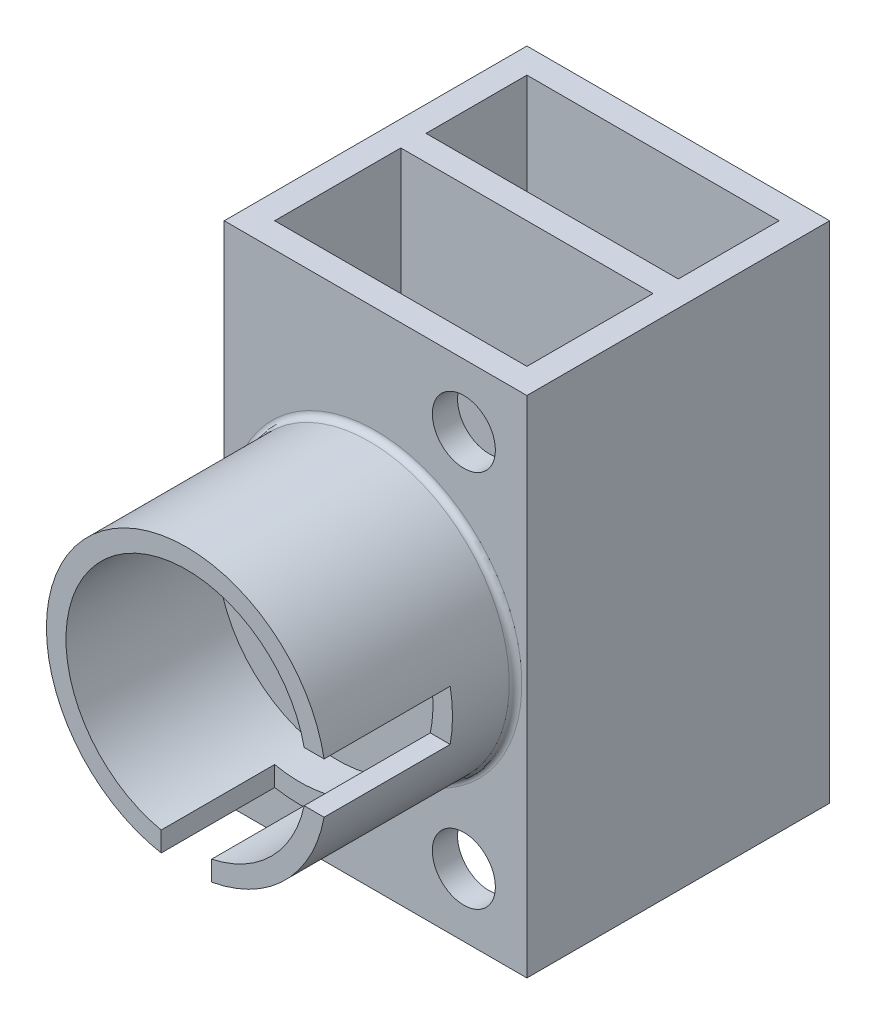
SolidWorks part; units mm, degrees
ref_plane "Front Plane" through (0, 0, 0) normal (0, 0, 1) x (1, 0, 0)
ref_plane "Top Plane" through (0, 0, 0) normal (0, 1, 0) x (1, 0, 0)
ref_plane "Right Plane" through (0, 0, 0) normal (1, 0, 0) x (0, 0, -1)
sketch "Sketch1" plane through (0, 0, 0) normal (0, 1, 0) x (1, 0, 0)
  line L1 (-12, -12) -> (12, -12)
  line L2 (-12, -12) -> (-12, 12)
  line L3 (-12, 12) -> (12, 12)
  line L4 (12, -12) -> (12, 12)
  line L5 (-12, -12) -> (12, 12) construction
  line L6 (-12, 12) -> (12, -12) construction
  point P0 (0, 0)
  dimension "D1" = 24
  dimension "D2" = 24
extrude "Boss-Extrude1" add sketch "Sketch1" along normal blind 40
shell "Shell3" thickness 2
sketch "Sketch2" plane through (0, 40, 0) normal (0, 1, 0) x (1, 0, 0)
  line L0 (-10, 10) -> (-10, -10) construction
  line L1 (-10, 0) -> (10, 0)
  line L2 (-10, 0) -> (-10, 2)
  line L3 (-10, 2) -> (10, 2)
  line L4 (10, 0) -> (10, 2)
  line L5 (10, -10) -> (10, 10) construction
  dimension "D1" = 2
  dimension "D2" = 10
sketch "Sketch3" plane through (0, 0, 12) normal (0, 0, 1) x (1, 0, 0)
  line L0 (-12, 0) -> (12, 0) construction
  line L1 (12, 40) -> (12, 0) construction
  circle A0 centre (0, 20) radius 11.1
  dimension "D2" = 22.2
  dimension "D1" = 20
  dimension "D3" = 12
extrude "Boss-Extrude3" add sketch "Sketch3" along normal blind 15
sketch "Sketch4" plane through (0, 0, 27) normal (0, 0, 1) x (1, 0, 0)
  line L0 (0, 31.1) -> (0, 8.9) construction
  line L1 (-11.1813, 20) -> (11.1, 20) construction
  circle A0 centre (0, 20) radius 11.1 construction
  circle A1 centre (0, 20) radius 9.55
  dimension "D1" = 19.1
extrude "Cut-Extrude3" cut sketch "Sketch4" against normal blind 12
fillet "Fillet4" radius 0.5 1 edges at (11.1, 20, 12)
extrude "Boss-Extrude5" add sketch "Sketch2" against normal blind 40
sketch "Sketch5" plane through (0, 0, 27) normal (0, 0, 1) x (1, 0, 0)
  line L0 (-11.1, 20) -> (11.1, 20) construction
  line L1 (0, 31.1) -> (0, 8.9) construction
  circle A0 centre (0, 20) radius 11.1 construction
ref_plane "Plane1" through (11.1, 0, 0) normal (1, 0, 0) x (0, 0, -1)
sketch "Sketch6" plane through (11.1, 0, 0) normal (1, 0, 0) x (0, 0, -1)
  line L1 (-17, 22) -> (-37, 22)
  line L2 (-17, 22) -> (-17, 18)
  line L3 (-17, 18) -> (-37, 18)
  line L4 (-37, 22) -> (-37, 18)
  line L5 (-17, 22) -> (-37, 18) construction
  line L6 (-17, 18) -> (-37, 22) construction
  point P0 (-27, 20)
  dimension "D1" = 4
  dimension "D2" = 20
extrude "Cut-Extrude4" cut sketch "Sketch6" against normal blind 8
ref_plane "Plane2" through (0, 8.9, 0) normal (0, 1, 0) x (1, 0, 0)
sketch "Sketch7" plane through (0, 8.9, 0) normal (0, 1, 0) x (1, 0, 0)
  line L1 (-2, -18) -> (2, -18)
  line L2 (-2, -18) -> (-2, -36)
  line L3 (-2, -36) -> (2, -36)
  line L4 (2, -18) -> (2, -36)
  line L5 (-2, -18) -> (2, -36) construction
  line L6 (-2, -36) -> (2, -18) construction
  point P0 (0, -27)
  dimension "D1" = 4
  dimension "D2" = 18
extrude "Cut-Extrude5" cut sketch "Sketch7" along normal blind 8
sketch "Sketch8" plane through (0, 0, 12) normal (0, 0, 1) x (1, 0, 0)
  line L0 (-12, 40) -> (12, 40) construction
  line L1 (12, 40) -> (12, 0) construction
  circle A0 centre (7, 35) radius 2.5
  point P2 (0, 0)
  point P5 (0, 0)
  point P7 (6.5234, 39.311)
  point P8 (4.924, 37.6347)
  dimension "D3" = 5
  dimension "D1" = 5
  dimension "D2" = 5
extrude "Cut-Extrude6" cut sketch "Sketch8" against normal up to next (2 mm away)
ref_plane "Plane3" through (0, 20, 0) normal (0, 1, 0) x (1, 0, 0)
mirror "Mirror1" about plane through (0, 20, 0) normal (0, 1, 0) of "Cut-Extrude6"
